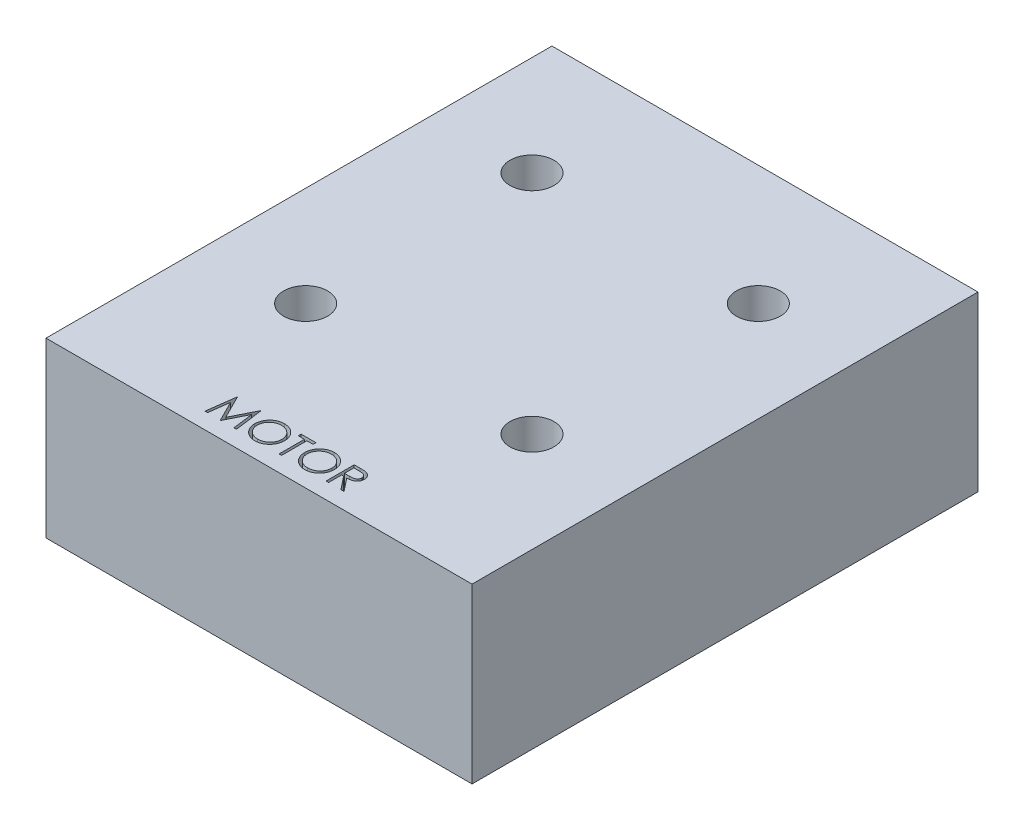
SolidWorks part; units mm, degrees
ref_plane "Front Plane" through (0, 0, 0) normal (0, 0, 1) x (1, 0, 0)
ref_plane "Top Plane" through (0, 0, 0) normal (0, 1, 0) x (1, 0, 0)
ref_plane "Right Plane" through (0, 0, 0) normal (1, 0, 0) x (0, 0, -1)
sketch "Sketch1" plane through (0, 0, 0) normal (0, 0, 1) x (1, 0, 0)
  line L0 (0, 0) -> (0, 13)
  line L3 (0, 13) -> (-16, 13)
  line L4 (-16, 13) -> (-16, 0)
  line L5 (-16, 0) -> (0, 0)
  dimension "D1" = 16
  dimension "D2" = 13
extrude "Boss-Extrude1" add sketch "Sketch1" along normal mid plane 38
sketch "Sketch2" plane through (0, 13, 0) normal (0, 1, 0) x (1, 0, 0)
  line L0 (0, 0) -> (-52, 0) construction
  line L1 (-52, 0) -> (-52, 20) construction
  line L2 (-52, 0) -> (-52, -20) construction
  dimension "D1" = 20
  dimension "D2" = 52
sketch "Sketch3" plane through (0, 13, 0) normal (0, 1, 0) x (1, 0, 0)
  line L0 (0, -19) -> (0, 19) construction
  line L1 (0, 10) -> (-8.5, 10) construction
  line L2 (0, 10) -> (0, -7) construction
  line L3 (0, -7) -> (-8.5, -7) construction
  line L4 (-8.5, 10) -> (-8.5, -7) construction
  line L5 (0, -19) -> (-16, -19) construction
  line L6 (-8.5, 1.5) -> (21.1723, 1.5) construction
  dimension "D1" = 8.5
  dimension "D2" = 17
  dimension "D3" = 12
hole_wizard "M4x0.7 Tapped Hole1" positions "Sketch6" profile "Sketch7" tap size "M4x0.7" standard "ANSI Metric"
sketch "Sketch6" plane through (0, 13, 0) normal (0, 1, 0) x (1, 0, 0)
  point P0 (-8.5, 10)
  point P3 (-8.5, -7)
sketch "Sketch7" plane through (-8.5, 13, -10) normal (1, 0, 0) x (0, 0, 1)
  line L0 (0, 0) -> (0, 8)
  line L1 (0, 8) -> (1.65, 8)
  line L2 (1.65, 8) -> (1.65, 0)
  line L5 (1.65, 0) -> (0, 0)
  line L10 (0, 8) -> (-1.65, 8) construction
  line L11 (0, -6.35) -> (0, 107.95) construction
  dimension "Tap Drill Dia." = 3.3
  dimension "Tap Drill Depth" = 8
  dimension "Drill Angle" = 180
cosmetic thread "Hole Thread1" parameters "D1"=8, "D2"=4
cosmetic thread "Hole Thread2" parameters "D1"=8, "D2"=4
mirror "Mirror1" about plane through (0, 0, 19) normal (-1, 0, 0) of bodies 105
cosmetic thread "Hole Thread3" parameters "D1"=8, "D2"=4
cosmetic thread "Hole Thread4" parameters "D1"=8, "D2"=4
sketch "Sketch9" plane through (0, 13, 0) normal (0, 1, 0) x (1, 0, 0)
  line L0 (-5.4416, -17.7797) -> (7.6321, -17.7797) construction
  text T0 "MOTOR" font "Century Gothic" height in points 8
extrude "Cut-Extrude1" cut sketch "Sketch9" against normal blind 1
ref_plane "SYMMETRY PLANE" through (0, 0, -1.5) normal (0, 0, 1) x (1, 0, 0)
sketch "Sketch10" plane through (0, 0, -19) normal (0, 0, -1) x (-1, 0, 0)
  circle A0 centre (0, 6.5712) radius 2.4643
